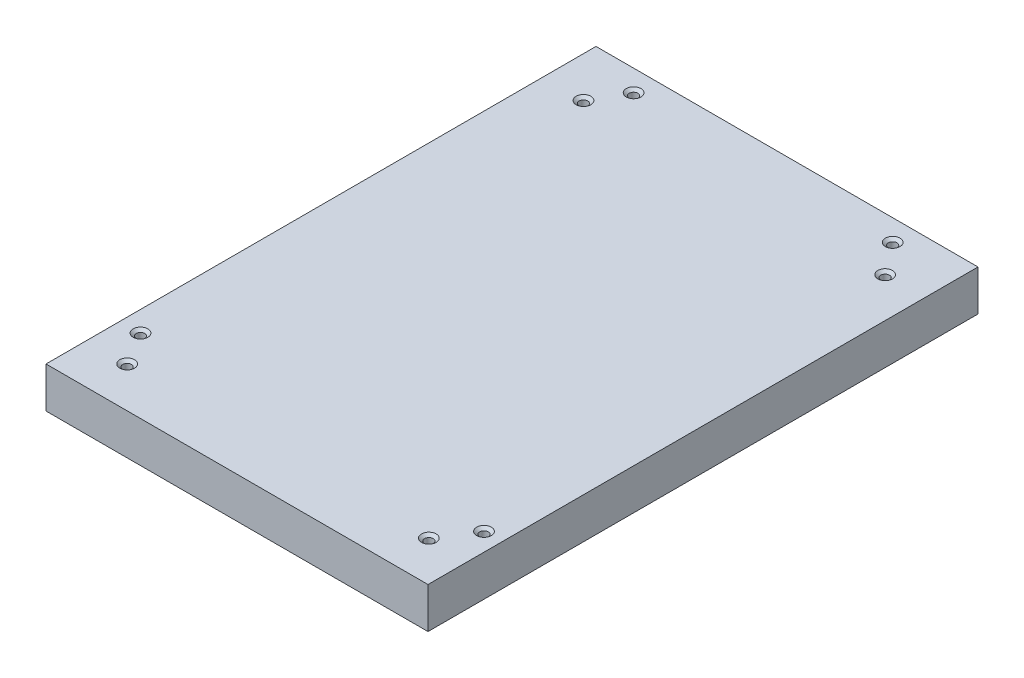
SolidWorks part; units mm, degrees
ref_plane "Front Plane" through (0, 0, 0) normal (0, 0, 1) x (1, 0, 0)
ref_plane "Top Plane" through (0, 0, 0) normal (0, 1, 0) x (1, 0, 0)
ref_plane "Right Plane" through (0, 0, 0) normal (1, 0, 0) x (0, 0, -1)
sketch "Sketch1" plane through (0, 0, 0) normal (0, 1, 0) x (1, 0, 0)
  line L1 (39.2686, -56.5409) -> (-39.2686, -56.5409)
  line L2 (39.2686, -56.5409) -> (39.2686, 56.5409)
  line L3 (39.2686, 56.5409) -> (-39.2686, 56.5409)
  line L4 (-39.2686, -56.5409) -> (-39.2686, 56.5409)
  line L5 (39.2686, -56.5409) -> (-39.2686, 56.5409) construction
  line L6 (39.2686, 56.5409) -> (-39.2686, -56.5409) construction
  point P0 (0, 0)
  dimension "D1" = 78.5373
  dimension "D2" = 113.0818
extrude "Boss-Extrude1" add sketch "Sketch1" along normal blind 8.382
hole_wizard "CSK for #0 Flat Head Machine Screw (100)1" positions "Sketch2" profile "Sketch3" countersink size "#0" standard "ANSI Inch" end condition through all
sketch "Sketch2" plane through (0, 8.382, 0) normal (0, 1, 0) x (1, 0, 0)
  point P0 (-30.9289, 45.6201)
  point P2 (31.1007, 45.6201)
  point P4 (31.1007, -48.1975)
  point P6 (-30.9289, -48.1975)
  point P8 (-35.0527, -41.3244)
  point P10 (35.5682, -41.3244)
  point P12 (26.1177, 52.1495)
  point P14 (-27.1487, 52.1495)
sketch "Sketch3" plane through (-30.9289, 8.382, -45.6201) normal (1, 0, 0) x (0, 0, 1)
  line L0 (0, 0) -> (0, 8.382)
  line L1 (0, 8.382) -> (0.889, 8.382)
  line L2 (0.889, 8.382) -> (0.889, 0.5222)
  line L3 (0.889, 0.5222) -> (1.5113, 0)
  line L5 (1.5113, 0) -> (0, 0)
  line L6 (-0.889, 0.5222) -> (-1.5113, 0) construction
  line L11 (0, -6.35) -> (0, 107.95) construction
  dimension "Thru Hole Dia." = 1.778
  dimension "Thru Hole Depth" = 8.382
  dimension "Near C'Sink Dia." = 3.0226
  dimension "Near C'Sink Angle" = 100
